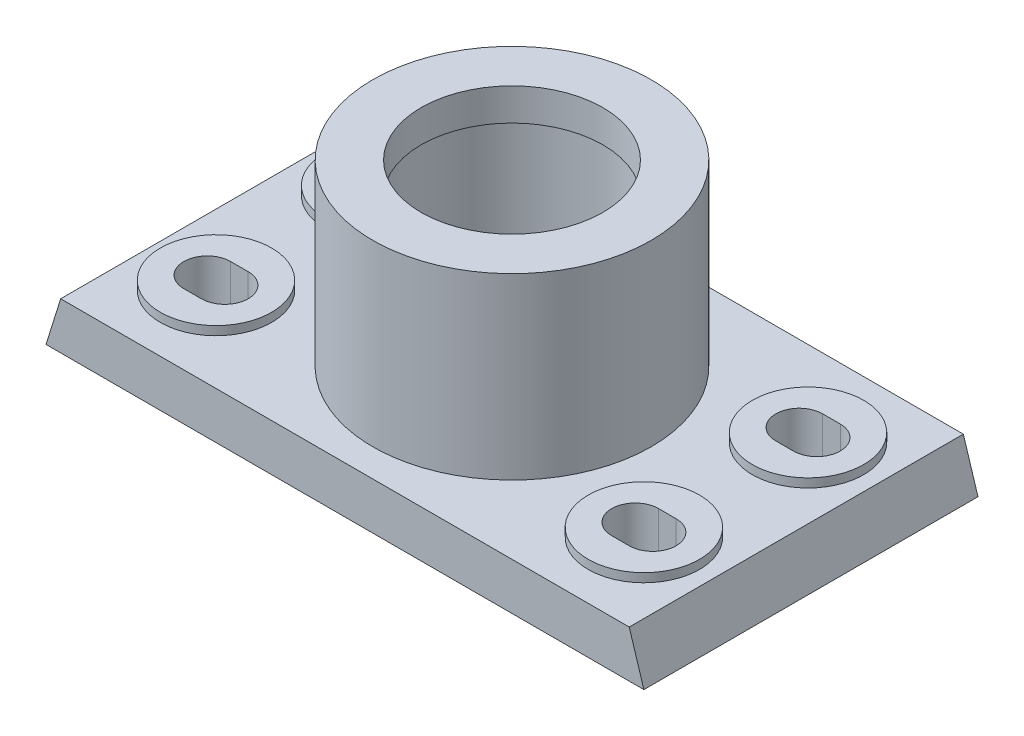
SolidWorks part; units mm, degrees
ref_plane "Front Plane" through (0, 0, 0) normal (0, 0, 1) x (1, 0, 0)
ref_plane "Top Plane" through (0, 0, 0) normal (0, 1, 0) x (1, 0, 0)
ref_plane "Right Plane" through (0, 0, 0) normal (1, 0, 0) x (0, 0, -1)
sketch "Sketch2" plane through (0, 0, 0) normal (0, 0, 1) x (1, 0, 0)
  line L0 (-145.7619, 0) -> (157.5205, 0) construction
  line L1 (0, 106.3818) -> (0, -101.0572) construction
  line L2 (-102, 0) -> (-97, 16)
  line L3 (-97, 16) -> (97, 16)
  line L4 (102, 0) -> (97, 16)
  line L5 (-102, 0) -> (102, 0)
  point P10 (0, 16)
  dimension "D1" = 204
  dimension "D2" = 16
  dimension "D3" = 5
extrude "Boss-Extrude1" add sketch "Sketch2" against normal blind 114
sketch "Sketch3" plane through (0, 0, 0) normal (0, -1, 0) x (1, 0, 0)
  line L0 (0, 26.2438) -> (0, -128.9097)
  line L1 (92, -104) -> (9.5, -104)
  line L2 (-92, -10) -> (-9.5, -10)
  line L3 (-92, -10) -> (-92, -104)
  line L4 (-92, -104) -> (-9.5, -104)
  line L5 (-9.5, -10) -> (-9.5, -104)
  line L6 (-92, -10) -> (-9.5, -104) construction
  line L7 (-92, -104) -> (-9.5, -10) construction
  line L8 (9.5, -10) -> (9.5, -104)
  line L9 (92, -10) -> (92, -104)
  line L10 (92, -10) -> (9.5, -10)
  point P2 (-50.75, -57)
  dimension "D1" = 82.5
  dimension "D2" = 10
  dimension "D3" = 47
  dimension "D4" = 57
  dimension "D5" = 9.5
extrude "Cut-Extrude1" cut sketch "Sketch3" against normal blind 3 contours L5 L2 L3 L4 | L9 L10 L8 L1
sketch "Sketch4" plane through (0, 16, 0) normal (0, 1, 0) x (1, 0, 0)
  line L0 (-76, 85) -> (-70, 85) construction
  line L1 (-76, 93) -> (-70, 93)
  line L2 (-76, 77) -> (-70, 77)
  line L3 (-102, 114) -> (-102, 0) construction
  line L4 (0, 0) -> (0, 136.1768)
  line L5 (-102, 57) -> (112.7959, 57)
  line L6 (76, 85) -> (70, 85) construction
  line L7 (76, 93) -> (70, 93)
  line L8 (76, 77) -> (70, 77)
  line L9 (76, 29) -> (70, 29) construction
  line L10 (76, 21) -> (70, 21)
  line L11 (76, 37) -> (70, 37)
  line L12 (-76, 29) -> (-70, 29) construction
  line L13 (-76, 21) -> (-70, 21)
  line L14 (-76, 37) -> (-70, 37)
  arc A0 (-76, 93) -> (-76, 77) centre (-76, 85) ccw
  arc A1 (-70, 77) -> (-70, 93) centre (-70, 85) ccw
  arc A2 (76, 93) -> (76, 77) centre (76, 85) cw
  arc A3 (70, 77) -> (70, 93) centre (70, 85) cw
  arc A4 (76, 21) -> (76, 37) centre (76, 29) ccw
  arc A5 (70, 37) -> (70, 21) centre (70, 29) ccw
  arc A6 (-76, 21) -> (-76, 37) centre (-76, 29) cw
  arc A7 (-70, 37) -> (-70, 21) centre (-70, 29) cw
  point P2 (-73, 85)
  point P7 (-102, 57)
  point P19 (73, 85)
  point P26 (73, 29)
  point P33 (-73, 29)
  dimension "D3" = 29
  dimension "D1" = 16
  dimension "D2" = 22
  dimension "D4" = 28
extrude "Cut-Extrude2" cut sketch "Sketch4" against normal through all contours L2 A1 L1 A0 | A3 L8 A2 L7 | A7 L14 A6 L13 | L11 A5 L10 A4
sketch "Sketch5" plane through (0, 16, 0) normal (0, 1, 0) x (1, 0, 0)
  line L0 (-102, 114) -> (-102, 0) construction
  line L1 (-102, 57) -> (135.4992, 57)
  line L2 (0, 0) -> (0, 134.5697)
  circle A0 centre (-73, 85) radius 19
  circle A1 centre (73, 85) radius 19
  circle A2 centre (-73, 29) radius 19
  circle A3 centre (73, 29) radius 19
  point P2 (-102, 57)
  line M1 (70, 37) -> (76, 37)
  arc M2 (76, 37) -> (76, 21) centre (76, 29) cw
  line M3 (76, 21) -> (70, 21)
  arc M4 (70, 21) -> (70, 37) centre (70, 29) cw
  line M5 (76, 77) -> (70, 77)
  arc M6 (70, 77) -> (70, 93) centre (70, 85) cw
  line M7 (70, 93) -> (76, 93)
  arc M8 (76, 93) -> (76, 77) centre (76, 85) cw
  line M9 (-70, 77) -> (-76, 77)
  arc M10 (-76, 77) -> (-76, 93) centre (-76, 85) cw
  line M11 (-76, 93) -> (-70, 93)
  arc M12 (-70, 93) -> (-70, 77) centre (-70, 85) cw
  line M17 (-76, 37) -> (-70, 37)
  arc M18 (-70, 37) -> (-70, 21) centre (-70, 29) cw
  line M19 (-70, 21) -> (-76, 21)
  arc M20 (-76, 21) -> (-76, 37) centre (-76, 29) cw
  dimension "D1" = 38
  dimension "D2" = 29
  dimension "D3" = 28
extrude "Boss-Extrude2" add sketch "Sketch5" along normal blind 3 contours A0 M12 M9 M10 M11 | A1 M8 M5 M6 M7 | A3 M4 M1 M2 M3 | A2 M20 M17 M18 M19
sketch "Sketch6" plane through (0, 16, 0) normal (0, 1, 0) x (1, 0, 0)
  circle A0 centre (0, 57) radius 31
  circle A1 centre (0, 57) radius 47.5
  dimension "D1" = 62
  dimension "D2" = 95
  dimension "D3" = 57
  dimension "D4" = 102
extrude "Boss-Extrude4" add sketch "Sketch6" along normal blind 61
ref_plane "Plane1" through (0, 0, -57) normal (0, 0, 1) x (1, 0, 0)
sketch "Sketch8" plane through (0, 0, -57) normal (0, 0, 1) x (1, 0, 0)
  line L0 (47.5, 77) -> (-47.5, 77) construction
  line L1 (-32.5, 66) -> (-29.5, 66)
  line L2 (-32.5, 66) -> (-32.5, 30.455)
  line L3 (-32.5, 30.455) -> (-29.5, 30.455)
  line L4 (-29.5, 66) -> (-29.5, 30.455)
  line L5 (0, 107.1062) -> (0, -5.921) construction
  dimension "D1" = 3
  dimension "D2" = 32.5
  dimension "D3" = 11
revolve "Cut-Revolve1" cut sketch "Sketch8" angle 360 about L5
sketch "Sketch9" plane through (0, 16, 0) normal (0, 1, 0) x (1, 0, 0)
  line L1 (-42.35, 57) -> (42.35, 57) construction
  circle A0 centre (-23.5, 57) radius 1.5
  dimension "D2" = 3
  dimension "D1" = 23.5
extrude "Cut-Extrude3" cut sketch "Sketch9" against normal blind 5
